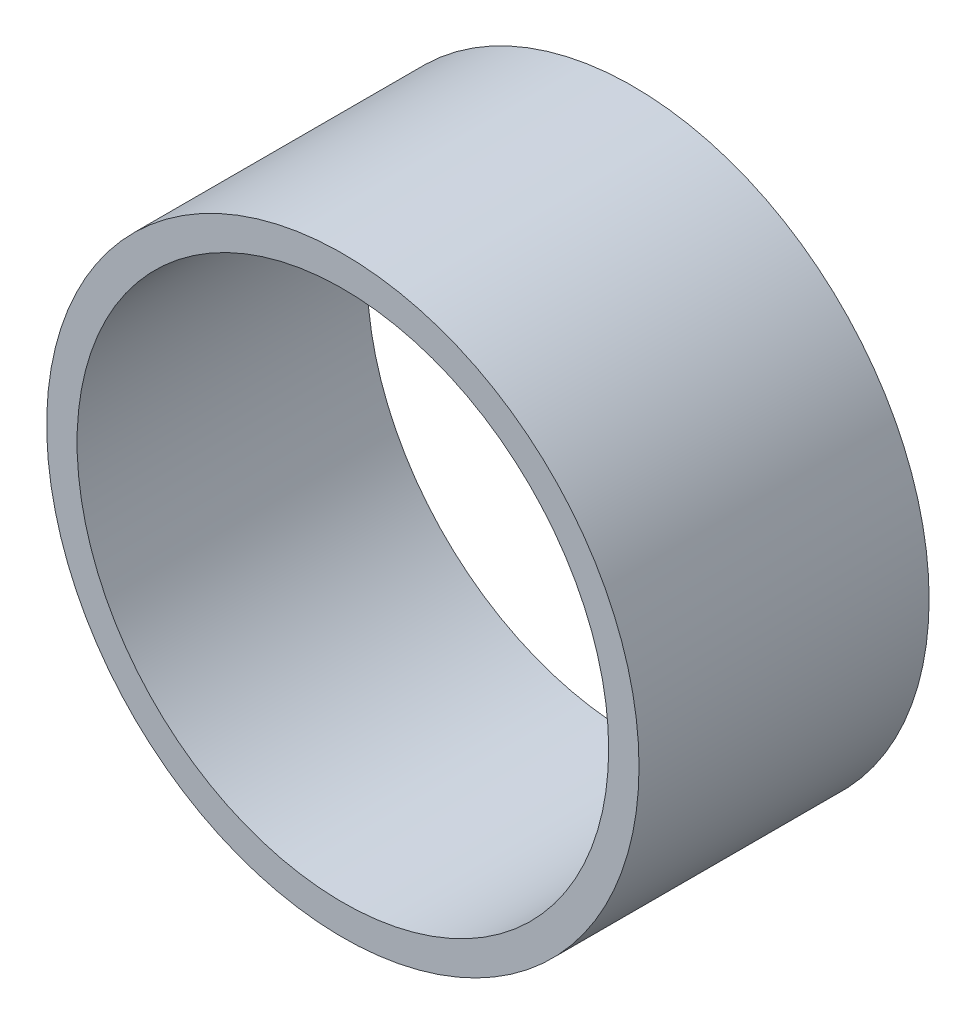
SolidWorks part; units mm, degrees
ref_plane "Front Plane" through (0, 0, 0) normal (0, 0, 1) x (1, 0, 0)
ref_plane "Top Plane" through (0, 0, 0) normal (0, 1, 0) x (1, 0, 0)
ref_plane "Right Plane" through (0, 0, 0) normal (1, 0, 0) x (0, 0, -1)
sketch "Sketch1" plane through (0, 0, 0) normal (0, 0, 1) x (1, 0, 0)
  circle A0 centre (0, 0) radius 2.5524
  circle A1 centre (0, 0) radius 2.2907
extrude "Boss-Extrude1" add sketch "Sketch1" along normal blind 2.5
